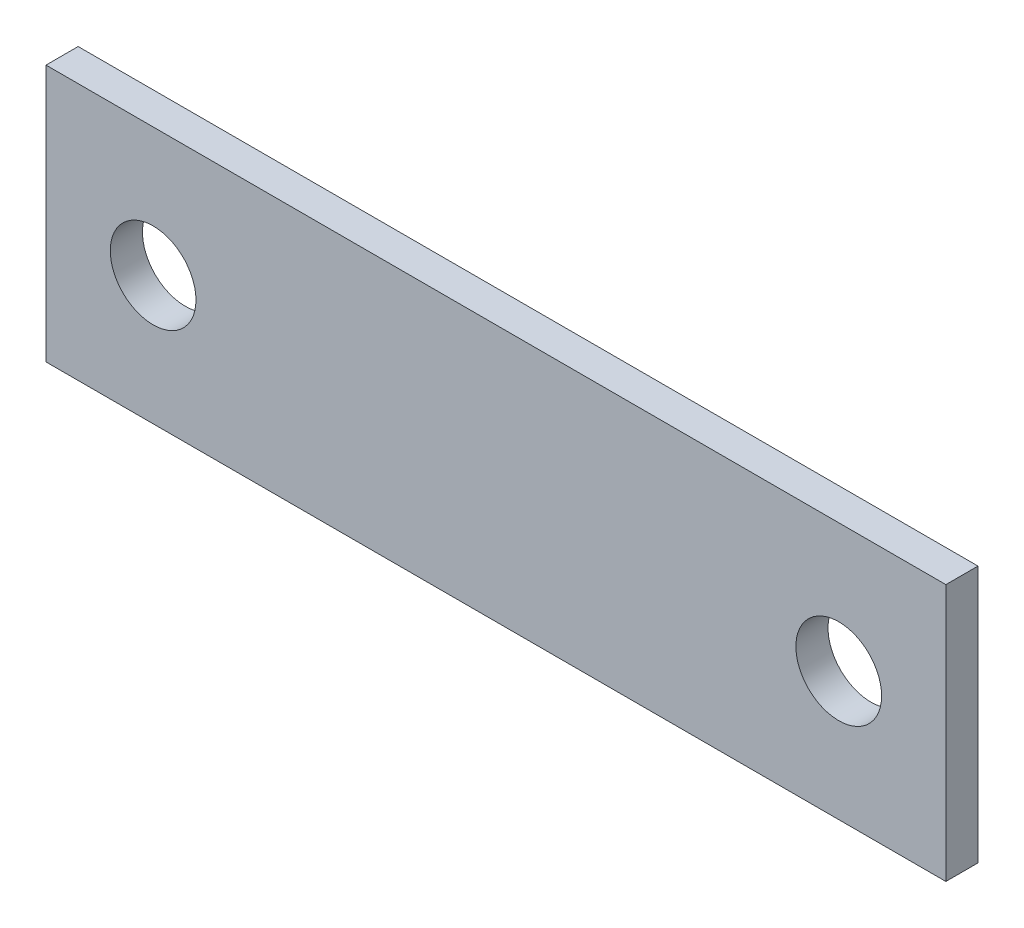
SolidWorks part; units mm, degrees
ref_plane "Front" through (0, 0, 0) normal (0, 0, 1) x (1, 0, 0)
ref_plane "Top" through (0, 0, 0) normal (0, 1, 0) x (1, 0, 0)
ref_plane "Right" through (0, 0, 0) normal (1, 0, 0) x (0, 0, -1)
sketch "Sketch1" plane through (0, 0, 0) normal (0, 0, 1) x (1, 0, 0)
  line L0 (25.4, 0) -> (-25.4, 0) construction
  line L1 (33.3375, -9.525) -> (-33.3375, -9.525)
  line L2 (33.3375, -9.525) -> (33.3375, 9.525)
  line L3 (33.3375, 9.525) -> (-33.3375, 9.525)
  line L4 (-33.3375, -9.525) -> (-33.3375, 9.525)
  line L5 (33.3375, -9.525) -> (-33.3375, 9.525) construction
  line L6 (33.3375, 9.525) -> (-33.3375, -9.525) construction
  circle A0 centre (-25.4, 0) radius 3.175
  circle A1 centre (25.4, 0) radius 3.175
  point P0 (0, 0)
  dimension "Hole Size" = 6.35
  dimension "Length" = 66.675
  dimension "Width" = 19.05
  dimension "Center to Center " = 50.8
extrude "Boss-Extrude1" add sketch "Sketch1" along normal blind 2.3813
